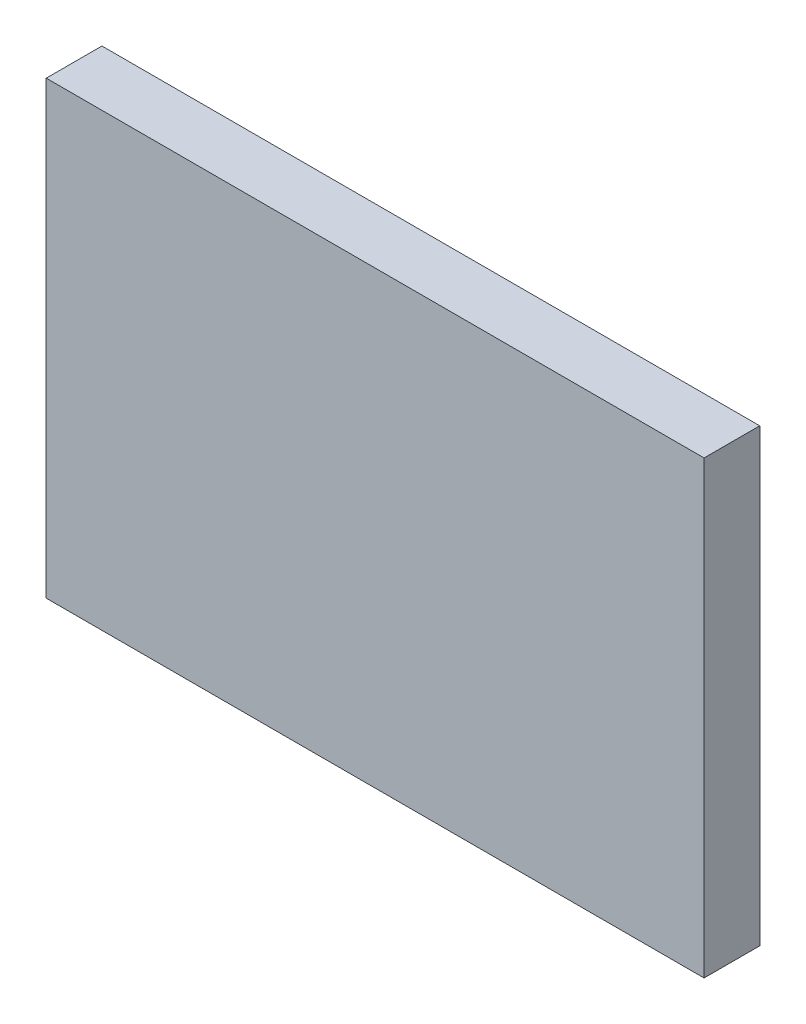
SolidWorks part; units mm, degrees
ref_plane "Front Plane" through (0, 0, 0) normal (0, 0, 1) x (1, 0, 0)
ref_plane "Top Plane" through (0, 0, 0) normal (0, 1, 0) x (1, 0, 0)
ref_plane "Right Plane" through (0, 0, 0) normal (1, 0, 0) x (0, 0, -1)
sketch "Sketch1" plane through (0, 0, 0) normal (0, 0, 1) x (1, 0, 0)
  line L1 (0, 0) -> (75, 0)
  line L2 (0, 0) -> (0, 51.35)
  line L3 (0, 51.35) -> (75, 51.35)
  line L4 (75, 0) -> (75, 51.35)
  dimension "D1" = 75
  dimension "D2" = 51.35
extrude "Boss-Extrude1" add sketch "Sketch1" along normal blind 6.35
